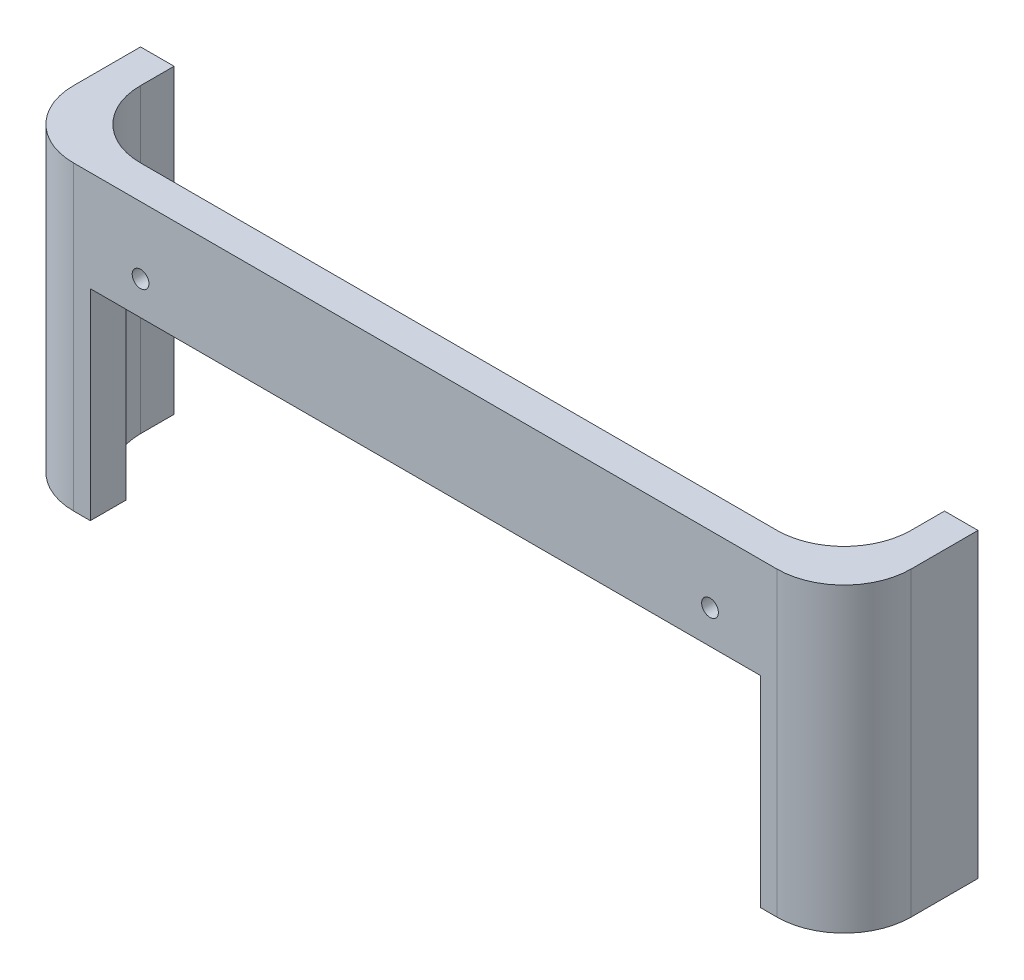
SolidWorks part; units mm, degrees
ref_plane "Front Plane" through (0, 0, 0) normal (0, 0, 1) x (1, 0, 0)
ref_plane "Top Plane" through (0, 0, 0) normal (0, 1, 0) x (1, 0, 0)
ref_plane "Right Plane" through (0, 0, 0) normal (1, 0, 0) x (0, 0, -1)
sketch "Sketch1" plane through (0, 0, 0) normal (0, 1, 0) x (1, 0, 0)
  line L1 (-125, -125) -> (125, -125)
  line L2 (-125, -125) -> (-125, 125)
  line L3 (-125, 125) -> (125, 125)
  line L4 (125, -125) -> (125, 125)
  line L5 (-115, -115) -> (115, -115)
  line L6 (-115, -115) -> (-115, 115)
  line L7 (-115, 115) -> (115, 115)
  line L8 (115, -115) -> (115, 115)
  line L9 (-115, -115) -> (115, 115) construction
  line L10 (-115, 115) -> (115, -115) construction
  point P0 (0, 0)
  point P6 (125, 0)
  point P7 (0, -125)
  point P8 (0, 0)
  dimension "D1" = 250
  dimension "D2" = 250
  dimension "D3" = 230
  dimension "D4" = 230
extrude "Boss-Extrude1" add sketch "Sketch1" along normal blind 90
sketch "Sketch2" plane through (0, 0, 125) normal (0, 0, 1) x (1, 0, 0)
  line L0 (-125, 0) -> (125, 0) construction
  line L1 (-100, 60) -> (100, 60)
  line L2 (-100, 60) -> (-100, 0)
  line L3 (-100, 0) -> (100, 0)
  line L4 (100, 60) -> (100, 0)
  line L6 (-125, 90) -> (125, 90) construction
  point P6 (0, 60)
  dimension "D1" = 200
  dimension "D2" = 30
extrude "Cut-Extrude1" cut sketch "Sketch2" against normal blind 50
fillet "Fillet1" radius 20 8 edges at (-115, 45, 115) (115, 45, 115) (115, 45, -115) (-115, 45, -115) (-125, 45, 125) (125, 45, 125) (125, 45, -125) (-125, 45, -125)
sketch "Sketch10" plane through (125, 0, 0) normal (1, 0, 0) x (0, 0, -1)
  line L0 (-105, 0) -> (105, 0) construction
  line L1 (-85, 0) -> (125, 0)
  line L2 (-85, 0) -> (-85, 90)
  line L3 (-85, 90) -> (125, 90)
  line L4 (125, 0) -> (125, 90)
  dimension "D1" = 210
extrude "Cut-Extrude6" cut sketch "Sketch10" against normal through all both and the other way through all
sketch "Sketch11" plane through (0, 0, 125) normal (0, 0, 1) x (1, 0, 0)
  line L0 (-85, 70) -> (85, 70) construction
  line L2 (-105, 90) -> (105, 90) construction
  circle A0 centre (-85, 70) radius 2.5
  circle A1 centre (85, 70) radius 2.5
  point P4 (0, 70)
  dimension "D1" = 5
  dimension "D2" = 5
  dimension "D3" = 20
  dimension "D4" = 170
extrude "Cut-Extrude7" cut sketch "Sketch11" against normal blind 10
